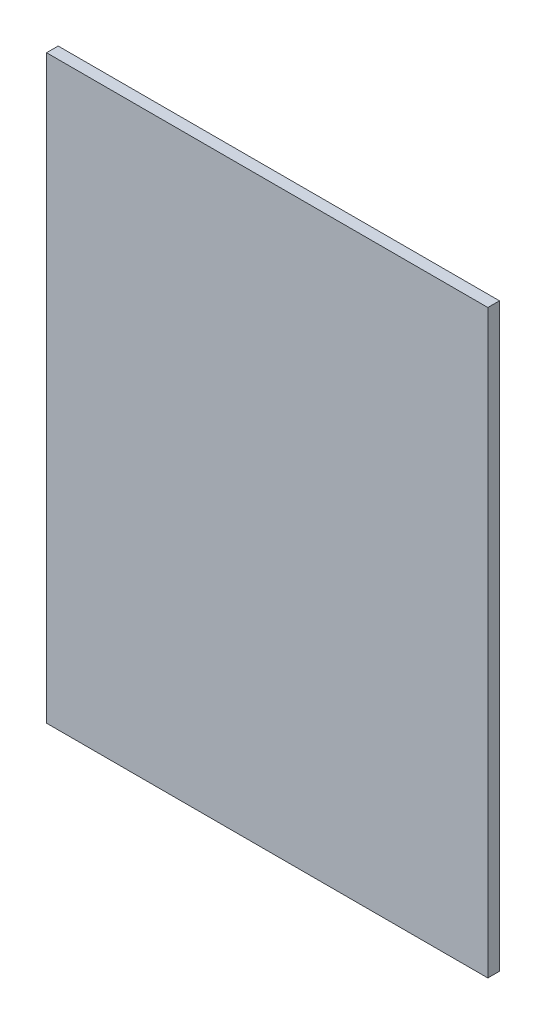
SolidWorks part; units mm, degrees
ref_plane "Plan de face" through (0, 0, 0) normal (0, 0, 1) x (1, 0, 0)
ref_plane "Plan de dessus" through (0, 0, 0) normal (0, 1, 0) x (1, 0, 0)
ref_plane "Plan de droite" through (0, 0, 0) normal (1, 0, 0) x (0, 0, -1)
sketch "Esquisse1" plane through (0, 0, 0) normal (0, 0, 1) x (1, 0, 0)
  line L0 (0, 0) -> (0, 250)
  line L1 (190, 250) -> (0, 250)
  line L2 (190, 250) -> (190, 0)
  line L3 (190, 0) -> (0, 0)
extrude "Boss.-Extru.2" add sketch "Esquisse1" along normal blind 5
